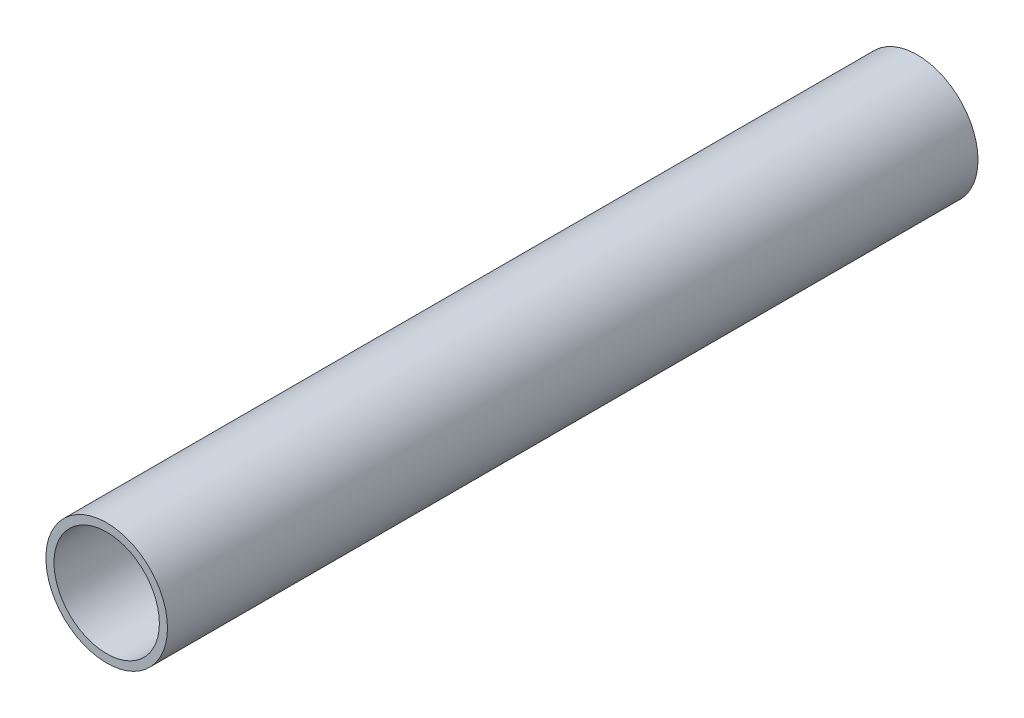
SolidWorks part; units mm, degrees
material "1060 Alloy"
ref_plane "Front Plane" through (0, 0, 0) normal (0, 0, 1) x (1, 0, 0)
ref_plane "Top Plane" through (0, 0, 0) normal (0, 1, 0) x (1, 0, 0)
ref_plane "Right Plane" through (0, 0, 0) normal (1, 0, 0) x (0, 0, -1)
sketch "Sketch1" plane through (0, 0, 0) normal (0, 0, 1) x (1, 0, 0)
  circle A1 centre (0, 0) radius 75
  dimension "D1" = 150
extrude "Boss-Extrude1" add sketch "Sketch1" along normal blind 1000
sketch "Sketch2" plane through (0, 0, 1000) normal (0, 0, 1) x (1, 0, 0)
  circle A2 centre (0, 0) radius 65
  dimension "D1" = 130
extrude "Cut-Extrude1" cut sketch "Sketch2" against normal blind 1000
equation "\"t\"= 0.01m'wall thickness"
equation "\"r\"= 0.15m - 2 * \"t\"'radius of inner diameter"
equation "\"D1@Sketch2\"=\"r\""
